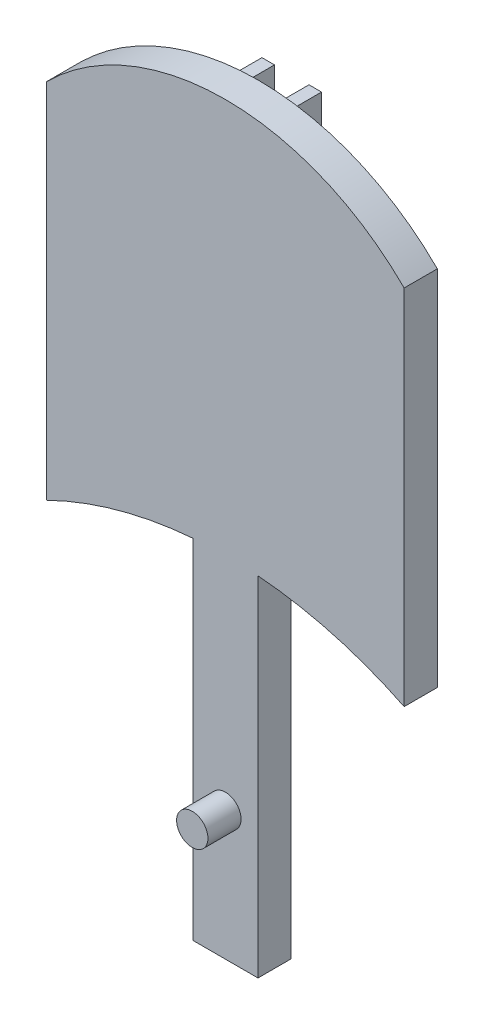
SolidWorks part; units mm, degrees
ref_plane "Front Plane" through (0, 0, 0) normal (0, 0, 1) x (1, 0, 0)
ref_plane "Top Plane" through (0, 0, 0) normal (0, 1, 0) x (1, 0, 0)
ref_plane "Right Plane" through (0, 0, 0) normal (1, 0, 0) x (0, 0, -1)
sketch "Sketch1" plane through (0, 0, 0) normal (0, 0, 1) x (1, 0, 0)
  line L1 (-17.1143, -17.3576) -> (17.1143, -17.3576)
  line L2 (-17.1143, -17.3576) -> (-17.1143, 17.3576)
  line L3 (-17.1143, 17.3576) -> (17.1143, 17.3576)
  line L4 (17.1143, -17.3576) -> (17.1143, 17.3576)
  line L5 (-17.1143, -17.3576) -> (17.1143, 17.3576) construction
  line L6 (-17.1143, 17.3576) -> (17.1143, -17.3576) construction
  arc A2 (-17.1143, 17.3576) -> (17.1143, 17.3576) centre (0, 0.1943) cw
  arc A3 (-17.1143, -17.3576) -> (17.1143, -17.3576) centre (0, -52.2147) cw
  point P0 (0, 0)
extrude "Boss-Extrude1" add sketch "Sketch1" along normal blind 3.175 contours A2 L3 | L2 A3 L4 L3
sketch "Sketch2" plane through (0, 0, 0) normal (0, 0, -1) x (-1, 0, 0)
  line L0 (1.6513, 22.2683) -> (1.6513, 23.2984)
  line L1 (-1.6513, -22.2683) -> (1.6513, -22.2683)
  line L2 (-1.6513, -22.2683) -> (-1.6513, 22.2683)
  line L3 (-1.6513, 22.2683) -> (1.6513, 22.2683)
  line L4 (1.6513, -22.2683) -> (1.6513, 22.2683)
  line L5 (-1.6513, -22.2683) -> (1.6513, 22.2683) construction
  line L6 (-1.6513, 22.2683) -> (1.6513, -22.2683) construction
  line L7 (-2.8534, -23.2984) -> (2.8534, -23.2984)
  line L8 (-2.8534, -23.2984) -> (-2.8534, 23.2984)
  line L9 (-2.8534, 23.2984) -> (2.8534, 23.2984)
  line L10 (2.8534, -23.2984) -> (2.8534, 23.2984)
  line L11 (-2.8534, -23.2984) -> (2.8534, 23.2984) construction
  line L12 (-2.8534, 23.2984) -> (2.8534, -23.2984) construction
  line L13 (-1.6513, 22.2683) -> (-1.6513, 23.2984)
  arc A0 (17.1143, -17.3576) -> (-17.1143, -17.3576) centre (0, -52.2147) ccw construction
  arc A1 (17.1143, -17.3576) -> (-17.1143, -17.3576) centre (0, -52.2147) ccw
  point P0 (0, 0)
  point P5 (0, 0)
  arc M3 (-17.1143, -17.3576) -> (17.1143, -17.3576) centre (0, -52.2147) cw
extrude "Boss-Extrude2" add sketch "Sketch2" along normal blind 3.175 contours L2 L13 L9 L8 M3 | L10 L9 L0 L4 M3
sketch "Sketch3" plane through (0, 0, 3.175) normal (0, 0, 1) x (1, 0, 0)
  line L0 (-3.1185, 0.3389) -> (3.1185, 0.3389)
  line L2 (-3.1185, 0.3389) -> (-3.1185, -46.8558)
  line L3 (-3.1185, -46.8558) -> (3.1185, -46.8558)
  line L4 (3.1185, 0.3389) -> (3.1185, -46.8558)
  line L5 (-0.0226, 0.3389) -> (3.1185, -46.8558) construction
  line L6 (-3.1185, -46.8558) -> (0.0226, 0.3389) construction
  point P0 (0, 0)
extrude "Boss-Extrude3" add sketch "Sketch3" against normal blind 3.175
sketch "Sketch4" plane through (0, 0, 3.175) normal (0, 0, 1) x (1, 0, 0)
  line L0 (0, -46.8558) -> (0, -34.5037)
  line L1 (-3.1185, -46.8558) -> (3.1185, -46.8558) construction
  circle A0 centre (0, -34.5037) radius 1.5
  dimension "D1" = 3
extrude "Boss-Extrude4" add sketch "Sketch4" along normal blind 3.175
sketch "Sketch5" plane through (0, 0, 6.35) normal (0, 0, 1) x (1, 0, 0)
  point P0 (0, -34.5037)
